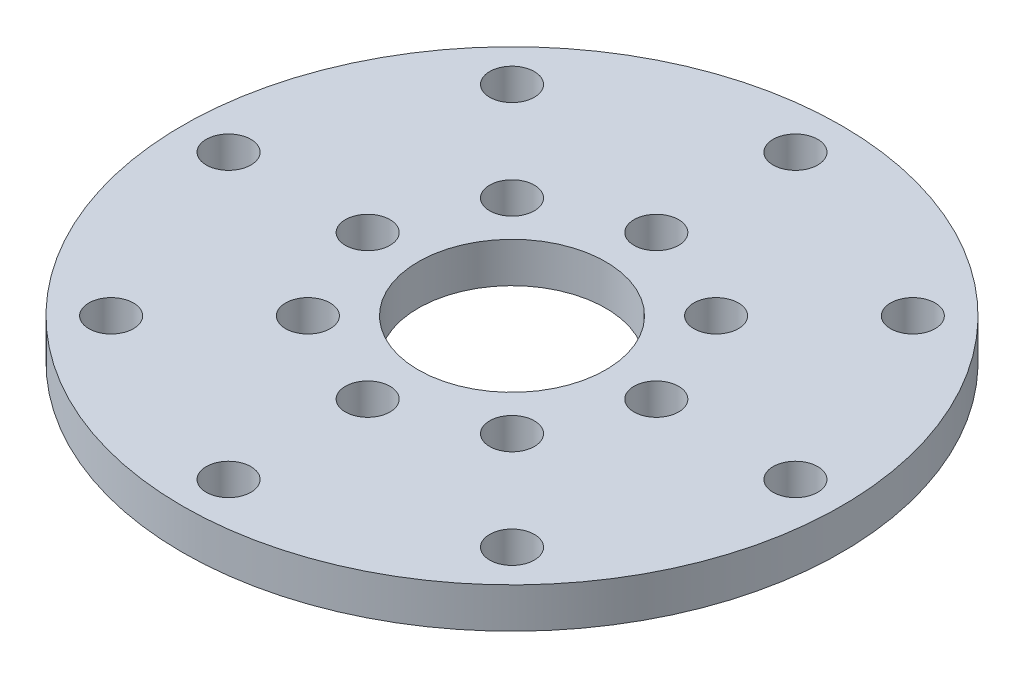
SolidWorks part; units mm, degrees
ref_plane "Alzado" through (0, 0, 0) normal (0, 0, 1) x (1, 0, 0)
ref_plane "Planta" through (0, 0, 0) normal (0, 1, 0) x (1, 0, 0)
ref_plane "Vista lateral" through (0, 0, 0) normal (1, 0, 0) x (0, 0, -1)
sketch "Croquis1" plane through (0, 0, 0) normal (0, 1, 0) x (1, 0, 0)
  line L0 (0, 22.15) -> (0, -22.15) construction
  circle A0 centre (0, 0) radius 22.15
  circle A1 centre (0, 0) radius 6.3
  circle A2 centre (0, 19.05) radius 1.5
  circle A3 centre (13.4704, 13.4704) radius 1.5
  circle A4 centre (19.05, 0) radius 1.5
  circle A5 centre (13.4704, -13.4704) radius 1.5
  circle A6 centre (0, -19.05) radius 1.5
  circle A7 centre (-13.4704, -13.4704) radius 1.5
  circle A8 centre (-19.05, 0) radius 1.5
  circle A9 centre (-13.4704, 13.4704) radius 1.5
  circle A10 centre (0, 9.7) radius 1.5
  circle A11 centre (6.8589, 6.8589) radius 1.5
  circle A12 centre (9.7, 0) radius 1.5
  circle A13 centre (6.8589, -6.8589) radius 1.5
  circle A14 centre (0, -9.7) radius 1.5
  circle A15 centre (-6.8589, -6.8589) radius 1.5
  circle A16 centre (-9.7, 0) radius 1.5
  circle A17 centre (-6.8589, 6.8589) radius 1.5
  point P24 (0, 0)
  point P41 (0, 0)
  dimension "D1" = 44.3
  dimension "D2" = 12.6
  dimension "D3" = 3
  dimension "D6" = 3
  dimension "D4" = 19.05
  dimension "D7" = 9.7
  dimension "D5" = 8
  dimension "D8" = 8
extrude "Saliente-Extruir1" add sketch "Croquis1" along normal blind 2.7
